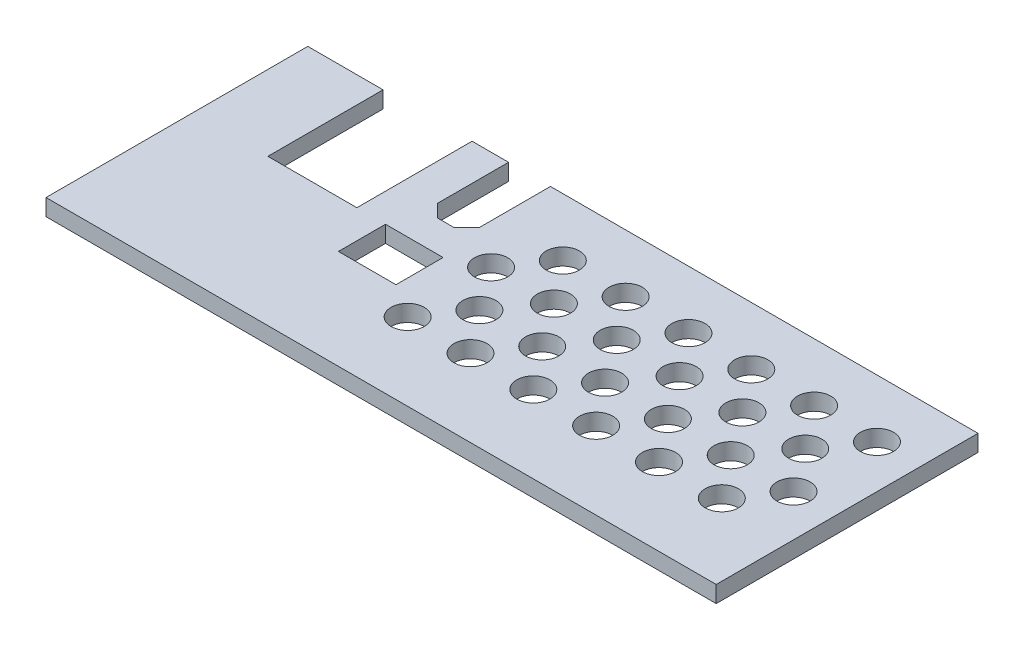
SolidWorks part; units mm, degrees
ref_plane "Front Plane" through (0, 0, 0) normal (0, 0, 1) x (1, 0, 0)
ref_plane "Top Plane" through (0, 0, 0) normal (0, 1, 0) x (1, 0, 0)
ref_plane "Right Plane" through (0, 0, 0) normal (1, 0, 0) x (0, 0, -1)
sketch "Sketch1" plane through (0, 0, 0) normal (0, 1, 0) x (1, 0, 0)
  line L8 (-20.4106, -5.3173) -> (-31.4106, -5.3173)
  line L9 (-20.4106, -14.3173) -> (-20.4106, -5.3173)
  line L10 (-31.4106, -14.3173) -> (-20.4106, -14.3173)
  line L11 (-31.4106, -5.3173) -> (-31.4106, -14.3173)
  line L38 (-68.2535, 16.6827) -> (-68.2535, -31.3173)
  line L39 (-68.2535, -31.3173) -> (57.7465, -31.3173)
  line L40 (57.7465, -31.3173) -> (57.7465, -18.0673)
  line L41 (57.7465, -18.0673) -> (35.7465, -18.0673)
  line L42 (35.7465, -18.0673) -> (35.7465, 5.9327)
  line L43 (35.7465, 5.9327) -> (57.7465, 5.9327)
  line L44 (57.7465, 5.9327) -> (57.7465, 16.6827)
  line L45 (57.7465, 16.6827) -> (-21.9106, 16.6827)
  line L46 (-21.9106, 16.6827) -> (-21.9106, 3.0827)
  line L47 (-21.9106, 3.0827) -> (-24.3106, 0.6827)
  line L48 (-24.3106, 0.6827) -> (-27.5106, 0.6827)
  line L49 (-27.5106, 0.6827) -> (-29.9106, 3.0827)
  line L50 (-29.9106, 3.0827) -> (-29.9106, 16.6827)
  line L51 (-29.9106, 16.6827) -> (-36.878, 16.6827)
  line L52 (-36.878, 16.6827) -> (-36.878, -5.3173)
  line L53 (-36.878, -5.3173) -> (-53.878, -5.3173)
  line L54 (-53.878, -5.3173) -> (-53.878, 16.6827)
  line L55 (-53.878, 16.6827) -> (-68.2535, 16.6827)
extrude "Boss-Extrude1" add sketch "Sketch1" along normal blind 3.175
sketch "Sketch2" plane through (0, 3.175, 0) normal (0, 1, 0) x (1, 0, 0)
  line L1 (-68.2535, 16.6827) -> (57.7465, 16.6827)
  line L2 (-68.2535, 16.6827) -> (-68.2535, -31.3173)
  line L3 (-68.2535, -31.3173) -> (57.7465, -31.3173)
  line L4 (57.7465, 16.6827) -> (57.7465, -31.3173)
  line L5 (-68.2535, 16.6827) -> (59.7465, 16.6827)
  line L6 (-68.2535, 16.6827) -> (-68.2535, -33.3173)
  line L7 (-68.2535, -33.3173) -> (59.7465, -33.3173)
  line L8 (59.7465, 16.6827) -> (59.7465, -33.3173)
  line M11 (-68.2535, -31.3173) -> (57.7465, -31.3173)
  line M12 (57.7465, -31.3173) -> (57.7465, -18.0673)
  line M16 (57.7465, 5.9327) -> (57.7465, 16.6827)
  dimension "D1" = 2
  dimension "D2" = 2
  dimension "D3" = 0
  dimension "D4" = 0
extrude "Boss-Extrude2" add sketch "Sketch2" against normal blind 3.175 contours L8 L5 L4 L6 L7 M16 M12 M11
sketch "Sketch3" plane through (0, 3.175, 0) normal (0, 1, 0) x (1, 0, 0)
  line L1 (30.7808, 10.0339) -> (58.5162, 10.0339)
  line L2 (30.7808, 10.0339) -> (30.7808, -19.6826)
  line L3 (30.7808, -19.6826) -> (58.5162, -19.6826)
  line L4 (58.5162, 10.0339) -> (58.5162, -19.6826)
extrude "Boss-Extrude3" add sketch "Sketch3" against normal blind 3.175
sketch "Sketch4" plane through (0, 3.175, 0) normal (0, 1, 0) x (1, 0, 0)
  circle A0 centre (-8.4798, 5.6114) radius 3.175
  circle A1 centre (3.5202, 5.6114) radius 3.175
  circle A2 centre (15.5202, 5.6114) radius 3.175
  circle A3 centre (27.5202, 5.6114) radius 3.175
  circle A4 centre (39.5202, 5.6114) radius 3.175
  circle A5 centre (51.5202, 5.6114) radius 3.175
  circle A6 centre (-14.2048, -2.3616) radius 3.175
  circle A7 centre (-2.2048, -2.3616) radius 3.175
  circle A8 centre (9.7952, -2.3616) radius 3.175
  circle A9 centre (21.7952, -2.3616) radius 3.175
  circle A10 centre (33.7952, -2.3616) radius 3.175
  circle A11 centre (45.7952, -2.3616) radius 3.175
  circle A12 centre (-8.2444, -10.5567) radius 3.175
  circle A13 centre (3.7556, -10.5567) radius 3.175
  circle A14 centre (15.7556, -10.5567) radius 3.175
  circle A15 centre (27.7556, -10.5567) radius 3.175
  circle A16 centre (39.7556, -10.5567) radius 3.175
  circle A17 centre (51.7556, -10.5567) radius 3.175
  circle A18 centre (-13.9693, -18.5296) radius 3.175
  circle A19 centre (-1.9693, -18.5296) radius 3.175
  circle A20 centre (10.0307, -18.5296) radius 3.175
  circle A21 centre (22.0307, -18.5296) radius 3.175
  circle A22 centre (34.0307, -18.5296) radius 3.175
  circle A23 centre (46.0307, -18.5296) radius 3.175
  dimension "D1" = 6.35
  dimension "D2" = 6
extrude "Cut-Extrude1" cut sketch "Sketch4" against normal blind 3.175
